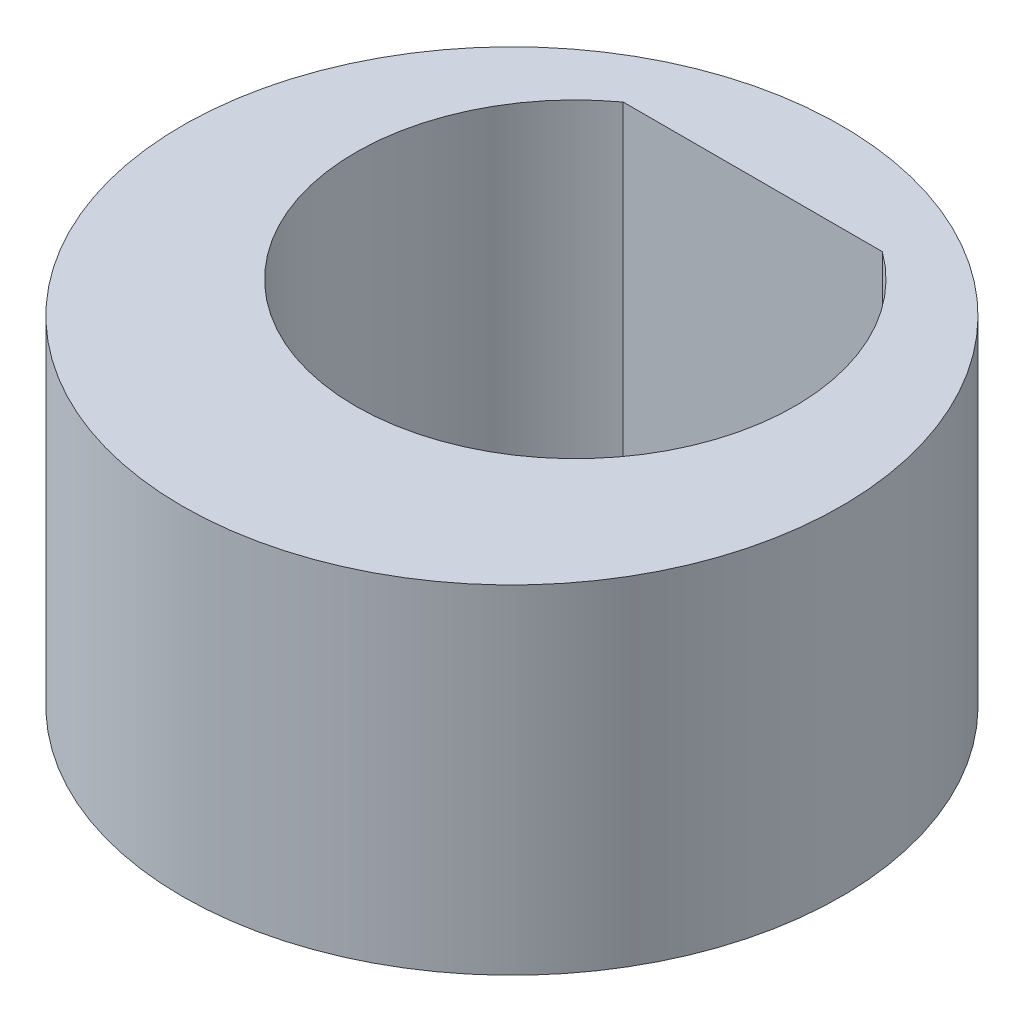
SolidWorks part; units mm, degrees
ref_plane "前视基准面" through (0, 0, 0) normal (0, 0, 1) x (1, 0, 0)
ref_plane "上视基准面" through (0, 0, 0) normal (0, 1, 0) x (1, 0, 0)
ref_plane "右视基准面" through (0, 0, 0) normal (1, 0, 0) x (0, 0, -1)
other "Configuration Table"
sketch "草图1" plane through (0, 0, 0) normal (0, 1, 0) x (1, 0, 0)
  line L0 (-1.533, 2.1) -> (1.533, 2.1)
  arc A0 (-1.533, 2.1) -> (1.533, 2.1) centre (0, 0) ccw
  circle A1 centre (0, -0.75) radius 3.9
  dimension "D1" = 7.8
  dimension "D2" = 5.2
  dimension "D3" = 0.75
  dimension "D4" = 2.1
extrude "凸台-拉伸1" add sketch "草图1" along normal blind 4
